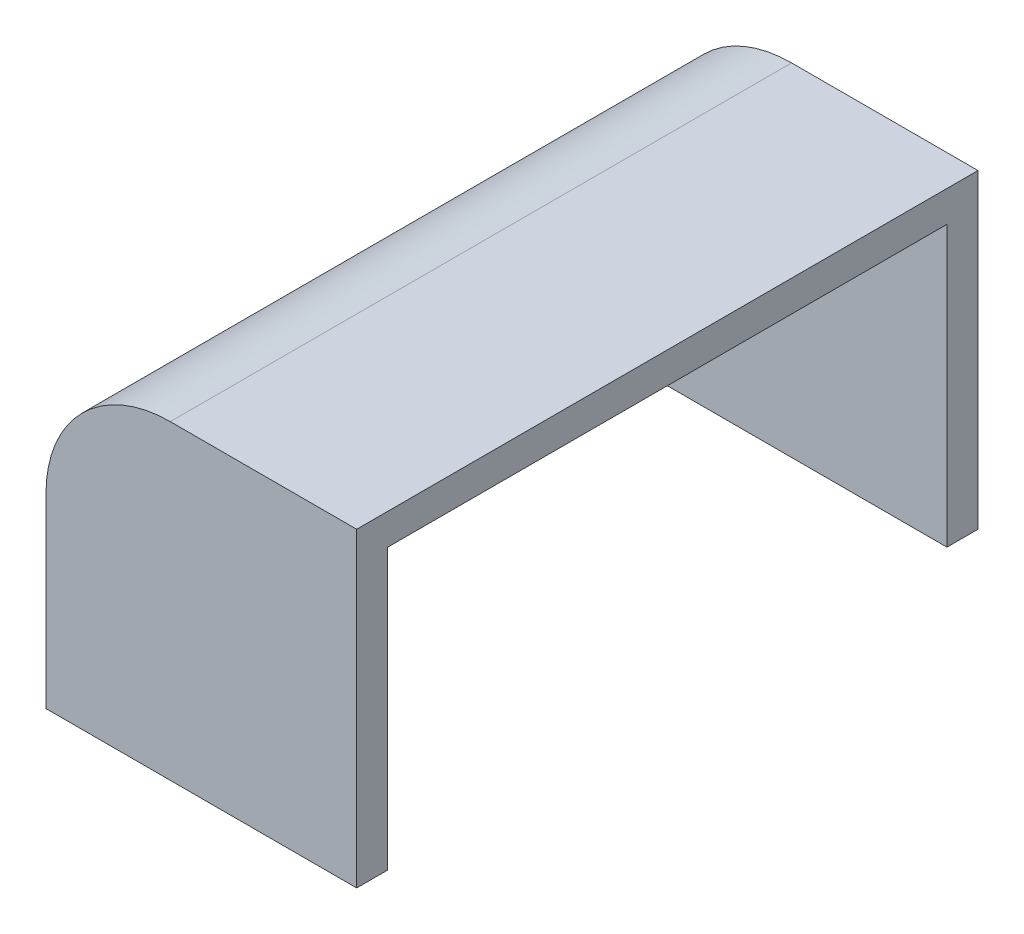
SolidWorks part; units mm, degrees
ref_plane "Plan de face" through (0, 0, 0) normal (0, 0, 1) x (1, 0, 0)
ref_plane "Plan de dessus" through (0, 0, 0) normal (0, 1, 0) x (1, 0, 0)
ref_plane "Plan de droite" through (0, 0, 0) normal (1, 0, 0) x (0, 0, -1)
sketch "Esquisse1" plane through (0, 0, 0) normal (0, 0, 1) x (1, 0, 0)
  line L0 (-5, 0) -> (-5, 3)
  line L1 (-3, 5) -> (0, 5)
  line L2 (0, 5) -> (0, 4.5)
  line L3 (0, 4.5) -> (-2.5, 4.5)
  line L4 (-4.5, 2.5) -> (-4.5, 0)
  line L5 (-4.5, 0) -> (-5, 0)
  arc A0 (-5, 3) -> (-3, 5) centre (-3, 3) cw
  arc A1 (-4.5, 2.5) -> (-2.5, 4.5) centre (-2.5, 2.5) cw
  dimension "D1" = 2
  dimension "D2" = 2
  dimension "D3" = 3
  dimension "D4" = 3
  dimension "D5" = 0.5
  dimension "D6" = 0.5
extrude "Boss.-Extru.1" add sketch "Esquisse1" along normal blind 9
sketch "Esquisse2" plane through (0, 0, 9) normal (0, 0, 1) x (1, 0, 0)
  line L0 (0, 5) -> (0, 0)
  line L1 (0, 0) -> (-5, 0)
  line L6 (-5, 0) -> (-4.5, 0)
  line L7 (-4.5, 0) -> (-4.5, 2.5)
  line L8 (-2.5, 4.5) -> (0, 4.5)
  line L9 (0, 4.5) -> (0, 5)
  line L10 (0, 5) -> (-3, 5)
  line L11 (-5, 3) -> (-5, 0)
  line L16 (0, 5) -> (-3, 5)
  line L17 (-5, 3) -> (-5, 0)
  arc A2 (-2.5, 4.5) -> (-4.5, 2.5) centre (-2.5, 2.5) ccw
  arc A3 (-3, 5) -> (-5, 3) centre (-3, 3) ccw
  arc A5 (-3, 5) -> (-5, 3) centre (-3, 3) ccw
  dimension "D1" = 0
extrude "Boss.-Extru.2" add sketch "Esquisse2" along normal blind 0.5
sketch "Esquisse3" plane through (0, 0, 0) normal (0, 0, -1) x (-1, 0, 0)
  line L0 (0, 5) -> (3, 5) construction
  line L1 (5, 3) -> (5, 0) construction
  line L2 (0, 5) -> (3, 5)
  line L3 (5, 3) -> (5, 0)
  line L4 (0, 5) -> (0, 0)
  line L5 (0, 0) -> (5, 0)
  arc A0 (5, 3) -> (3, 5) centre (3, 3) ccw construction
  arc A1 (5, 3) -> (3, 5) centre (3, 3) ccw
extrude "Boss.-Extru.3" add sketch "Esquisse3" along normal blind 0.5
